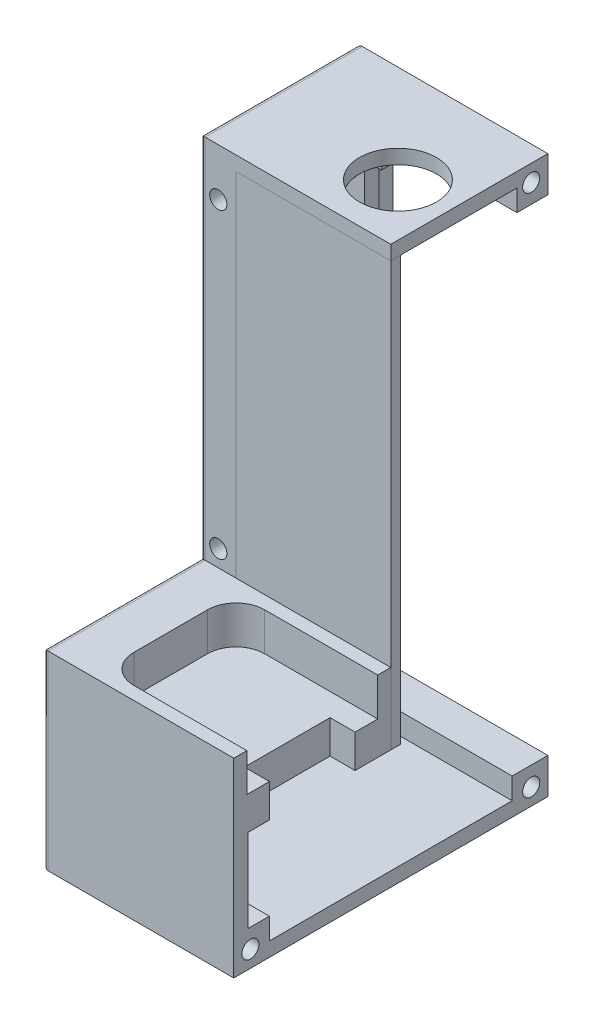
SolidWorks part; units mm, degrees
material "ABS"
ref_plane "Front" through (0, 0, 0) normal (0, 0, 1) x (1, 0, 0)
ref_plane "Top" through (0, 0, 0) normal (0, 1, 0) x (1, 0, 0)
ref_plane "Right" through (0, 0, 0) normal (1, 0, 0) x (0, 0, -1)
sketch "ｽｹｯﾁ1" plane through (0, 0, 0) normal (1, 0, 0) x (0, 0, -1)
  line L0 (23, 92) -> (0, 92)
  line L1 (33, 92) -> (23, 92)
  line L2 (33, 92) -> (33, -25)
  line L3 (33, -25) -> (23, -25)
  line L4 (23, 92) -> (23, -25)
  line L5 (0, 92) -> (0, -25)
  line L6 (0, -25) -> (23, -25)
  line L7 (0, -25) -> (-33, -25)
  line L8 (-33, -25) -> (-33, 0)
  line L9 (-33, 0) -> (0, 0)
  dimension "D1" = 117
  dimension "D2" = 10
  dimension "D3" = 33
  dimension "D4" = 23
  dimension "D5" = 25
extrude "ﾎﾞｽ - 押し出し1" add sketch "ｽｹｯﾁ1" along normal blind 60 contours L9 L8 L7 L5 | L5 L6 L4 L0 | L1 L4 L3 L2
sketch "ｽｹｯﾁ2" plane through (0, 0, -33) normal (0, 0, -1) x (-1, 0, 0)
  line L0 (-60, 92) -> (-60, -25) construction
  line L1 (-7.5, 22.5) -> (-52.5, 22.5)
  line L2 (-7.5, 22.5) -> (-7.5, 84.5)
  line L3 (-7.5, 84.5) -> (-52.5, 84.5)
  line L4 (-52.5, 22.5) -> (-52.5, 84.5)
  line L5 (-7.5, 22.5) -> (-52.5, 84.5) construction
  line L6 (-7.5, 84.5) -> (-52.5, 22.5) construction
  line L8 (0, 92) -> (0, -25) construction
  line L9 (-60, 92) -> (0, 92) construction
  point P0 (-30, 53.5)
  dimension "D1" = 62
  dimension "D2" = 7.5
  dimension "D3" = 7.5
  dimension "D4" = 7.5
extrude "ｶｯﾄ - 押し出し1" cut sketch "ｽｹｯﾁ2" against normal blind 10
sketch "ｽｹｯﾁ3" plane through (0, 92, 0) normal (0, 1, 0) x (1, 0, 0)
  line L1 (0, 33) -> (0, 0) construction
  line L2 (60, 0) -> (0, 0) construction
  circle A0 centre (29, 12.5) radius 8.1
  dimension "D1" = 16.2
  dimension "D2" = 29
  dimension "D3" = 12.5
extrude "ｶｯﾄ - 押し出し2" cut sketch "ｽｹｯﾁ3" against normal blind 10
sketch "ｽｹｯﾁ4" plane through (0, 0, -33) normal (0, 0, -1) x (-1, 0, 0)
  line L0 (-60, -25) -> (0, -25) construction
  line L1 (-7.5, 22.5) -> (-52.5, 22.5)
  line L2 (-7.5, 22.5) -> (-7.5, -17.5)
  line L3 (-7.5, -17.5) -> (-52.5, -17.5)
  line L4 (-52.5, 22.5) -> (-52.5, -17.5)
  line L7 (-60, 92) -> (-60, -25) construction
  dimension "D1" = 7.5
  dimension "D2" = 7.5
extrude "ｶｯﾄ - 押し出し3" cut sketch "ｽｹｯﾁ4" against normal offset from surface (58.5 mm away) 7.5 up to face at (30, -12.5, 33)
sketch "ｽｹｯﾁ5" plane through (0, 0, 0) normal (0, 1, 0) x (1, 0, 0)
  line L1 (41.75, -2.75) -> (16.25, -2.75)
  line L2 (47.75, -8.75) -> (47.75, -24.25)
  line L3 (41.75, -30.25) -> (16.25, -30.25)
  line L4 (10.25, -8.75) -> (10.25, -24.25)
  line L5 (47.75, -2.75) -> (10.25, -30.25) construction
  line L6 (47.75, -30.25) -> (10.25, -2.75) construction
  line L7 (0, -33) -> (0, 0) construction
  line L11 (60, -33) -> (0, -33)
  line L12 (60, -33) -> (60, 0)
  line L13 (60, 0) -> (0, 0)
  line L14 (0, -33) -> (0, 0)
  arc A0 (10.25, -8.75) -> (16.25, -2.75) centre (16.25, -8.75) cw
  arc A1 (47.75, -8.75) -> (41.75, -2.75) centre (41.75, -8.75) ccw
  arc A2 (47.75, -24.25) -> (41.75, -30.25) centre (41.75, -24.25) cw
  arc A3 (16.25, -30.25) -> (10.25, -24.25) centre (16.25, -24.25) cw
  point P0 (29, -16.5)
  dimension "D5" = 6
  dimension "D1" = 27.5
  dimension "D2" = 37.5
  dimension "D3" = 29
  dimension "D4" = 2.75
extrude "ﾎﾞｽ - 押し出し2" add sketch "ｽｹｯﾁ5" along normal blind 15
sketch "ｽｹｯﾁ6" plane through (0, 0, 0) normal (0, 1, 0) x (1, 0, 0)
  line L20 (34.75, -30.25) -> (34.75, -2.75)
  line L21 (42.75, -30.25) -> (42.75, -2.8339)
  line L22 (34.75, -25.5) -> (42.75, -25.5)
  line L24 (41.75, -2.75) -> (16.25, -2.75)
  line L25 (47.75, -24.25) -> (47.75, -8.75)
  line L26 (16.25, -30.25) -> (41.75, -30.25)
  line L27 (10.25, -8.75) -> (10.25, -24.25)
  line L28 (41.75, -2.75) -> (16.25, -2.75)
  line L29 (47.75, -24.25) -> (47.75, -8.75)
  line L30 (16.25, -30.25) -> (41.75, -30.25)
  line L31 (10.25, -8.75) -> (10.25, -24.25)
  line L32 (34.75, -7.5) -> (42.75, -7.5)
  arc A21 (16.25, -2.75) -> (10.25, -8.75) centre (16.25, -8.75) ccw
  arc A22 (47.75, -8.75) -> (41.75, -2.75) centre (41.75, -8.75) ccw
  arc A23 (41.75, -30.25) -> (47.75, -24.25) centre (41.75, -24.25) ccw
  arc A24 (10.25, -24.25) -> (16.25, -30.25) centre (16.25, -24.25) ccw
  arc A25 (16.25, -2.75) -> (10.25, -8.75) centre (16.25, -8.75) ccw
  arc A26 (47.75, -8.75) -> (41.75, -2.75) centre (41.75, -8.75) ccw
  arc A27 (41.75, -30.25) -> (47.75, -24.25) centre (41.75, -24.25) ccw
  arc A28 (10.25, -24.25) -> (16.25, -30.25) centre (16.25, -24.25) ccw
  arc M14 (10.3817, -25.5) -> (16.25, -30.25) centre (16.25, -24.25) ccw
  line M15 (16.25, -30.25) -> (41.75, -30.25)
  arc M16 (41.75, -30.25) -> (47.6183, -25.5) centre (41.75, -24.25) ccw
  line M17 (47.6183, -25.5) -> (10.3817, -25.5)
  dimension "D2" = 13
  dimension "D3" = 8
  dimension "D4" = 18
  dimension "D5" = 4.75
  dimension "D1" = 0
extrude "ﾎﾞｽ - 押し出し3" add sketch "ｽｹｯﾁ6" along normal blind 7 contours L31 A28 L20 L28 A25 M17 | L20 M15 M17 M14 | L21 L20 M16 M17 M15 | A27 L29 A26 L21 M17 | L21 M16 M17 | L21 A26 L28 L20 L32
sketch "ｽｹｯﾁ7" plane through (0, 0, 0) normal (0, 0, 1) x (1, 0, 0)
  line L0 (0, 92) -> (0, 15) construction
  line L1 (52.5, 89) -> (7.5, 89)
  line L2 (52.5, 89) -> (52.5, 22.5)
  line L3 (52.5, 22.5) -> (7.5, 22.5)
  line L4 (7.5, 89) -> (7.5, 22.5)
  line L5 (52.5, 89) -> (7.5, 22.5) construction
  line L6 (52.5, 22.5) -> (7.5, 89) construction
  line L7 (60, 92) -> (0, 92) construction
  line L9 (52.5, 22.5) -> (7.5, 22.5) construction
  line L11 (52.5, 22.5) -> (52.5, 15) construction
  point P0 (30, 55.75)
  dimension "D1" = 7.5
  dimension "D2" = 3
extrude "ｶｯﾄ - 押し出し4" cut sketch "ｽｹｯﾁ7" against normal offset from surface (20 mm away) 3 up to face at (30, 53.5, -23)
sketch "ｽｹｯﾁ8" plane through (0, 89, 0) normal (0, -1, 0) x (-1, 0, 0)
  line L1 (-7.5, 0) -> (-52.5, 0)
  line L2 (-7.5, 0) -> (-7.5, 2)
  line L3 (-7.5, 2) -> (-52.5, 2)
  line L4 (-52.5, 0) -> (-52.5, 2)
  line L6 (-52.5, 20) -> (-52.5, 0) construction
  dimension "D1" = 2
extrude "ﾎﾞｽ - 押し出し4" add sketch "ｽｹｯﾁ8" along normal up to vertex (89 mm away) separate body
sketch "ｽｹｯﾁ9" plane through (0, 0, 0) normal (-1, 0, 0) x (0, 0, 1)
  line L0 (-33, 92) -> (0, 92) construction
  line L1 (-33, 92) -> (-33, -25) construction
  line L2 (-33, -25) -> (33, -25) construction
  line L3 (33, -25) -> (33, 15) construction
  circle A0 centre (-29.5, 88.5) radius 1.8
  circle A1 centre (-29.5, -21.5) radius 1.8
  circle A2 centre (29.5, -21.5) radius 1.8
  dimension "D3" = 3.6
  dimension "D5" = 3.5
  dimension "D1" = 3.5
  dimension "D2" = 3.5
  dimension "D4" = 3.5
extrude "ｶｯﾄ - 押し出し5" cut sketch "ｽｹｯﾁ9" against normal through all
sketch "ｽｹｯﾁ10" plane through (0, 0, 0) normal (0, 0, 1) x (1, 0, 0)
  line L0 (60, 92) -> (0, 92) construction
  line L1 (7.5, 15) -> (0, 15) construction
  line L2 (0, 92) -> (0, 15) construction
  line L3 (60, 92) -> (60, 15) construction
  circle A0 centre (3.75, 82) radius 1.8
  circle A1 centre (56.25, 82) radius 1.8
  circle A2 centre (56.25, 18.5) radius 1.8
  circle A3 centre (3.75, 18.5) radius 1.8
  dimension "D3" = 3.6
  dimension "D1" = 3.5
  dimension "D2" = 10
  dimension "D4" = 3.75
  dimension "D5" = 3.75
extrude "ｶｯﾄ - 押し出し6" cut sketch "ｽｹｯﾁ10" against normal through all both and the other way through all
sketch "ｽｹｯﾁ12" plane through (0, 0, -23) normal (0, 0, -1) x (-1, 0, 0)
  line L0 (-52.5, 84.5) -> (-52.5, 22.5) construction
  line L2 (-7.5, 84.5) -> (-52.5, 84.5) construction
  circle A0 centre (-49, 81.5) radius 1.8
  circle A1 centre (-11, 81.5) radius 1.8
  circle A2 centre (-11, 39.5) radius 1.8
  circle A3 centre (-49, 39.5) radius 1.8
  dimension "D3" = 3.6
  dimension "D1" = 42
  dimension "D2" = 38
  dimension "D4" = 3.5
  dimension "D5" = 3
extrude "ｶｯﾄ - 押し出し7" cut sketch "ｽｹｯﾁ12" against normal up to next (3 mm away)
sketch "ｽｹｯﾁ15" plane through (60, 0, 0) normal (1, 0, 0) x (0, 0, -1)
  line L6 (0, 15) -> (-33, 15)
  line L13 (-33, 15) -> (-33, -25)
  line L14 (-33, -25) -> (33, -25)
  line L15 (33, -25) -> (33, 92)
  line L19 (-33, 15) -> (-33, -25)
  line L20 (-33, -25) -> (33, -25)
  line L21 (33, -25) -> (33, 92)
  line L26 (33, 92) -> (0, 92)
  line L28 (33, 92) -> (0, 92)
  line L30 (0, 15) -> (-33, 15)
  line L32 (0, 92) -> (0, 15)
  line L34 (0, 92) -> (0, 15)
  dimension "D1" = 0
extrude "ｶｯﾄ - 押し出し9" cut sketch "ｽｹｯﾁ15" against normal blind 20
sketch "ｽｹｯﾁ17" plane through (0, -17.5, 0) normal (0, 1, 0) x (1, 0, 0)
  line L0 (40, -25.5) -> (40, 33) construction
  line L1 (7.5, -25.5) -> (40, -25.5)
  line L2 (7.5, -25.5) -> (7.5, 25.5)
  line L3 (7.5, 25.5) -> (40, 25.5)
  line L4 (40, -25.5) -> (40, 25.5)
  line L5 (40, 33) -> (7.5, 33) construction
  dimension "D1" = 7.5
extrude "ｶｯﾄ - 押し出し11" cut sketch "ｽｹｯﾁ17" against normal offset from surface (4.5 mm away) 3 up to face at (20, -25, 0)
sketch "ｽｹｯﾁ18" plane through (0, 0, 25.5) normal (0, 0, -1) x (-1, 0, 0)
  line L0 (-40, 7) -> (-40, -22) construction
  line L1 (-7.5, 0) -> (-40, 0)
  line L2 (-7.5, 0) -> (-7.5, -17.5)
  line L3 (-7.5, -17.5) -> (-40, -17.5)
  line L4 (-40, 0) -> (-40, -17.5)
  line L6 (-40, -25) -> (0, -25) construction
  dimension "D1" = 7.5
extrude "ｶｯﾄ - 押し出し12" cut sketch "ｽｹｯﾁ18" against normal offset from surface (4.5 mm away) 3 up to face at (20, -5, 33)
sketch "ｽｹｯﾁ19" plane through (0, 0, -23) normal (0, 0, -1) x (-1, 0, 0)
  line L1 (-40, 84.5) -> (-14.5, 84.5)
  line L2 (-40, 84.5) -> (-40, 22.5)
  line L3 (-40, 22.5) -> (-14.5, 22.5)
  line L4 (-14.5, 84.5) -> (-14.5, 22.5)
  line L6 (-7.5, 22.5) -> (-7.5, 84.5) construction
  dimension "D1" = 7
extrude "ｶｯﾄ - 押し出し13" cut sketch "ｽｹｯﾁ19" against normal up to next (3 mm away)
sketch "ｽｹｯﾁ20" plane through (40, 0, 0) normal (1, 0, 0) x (0, 0, -1)
  line L0 (20, 84.5) -> (33, 84.5) construction
  line L1 (20, 89) -> (26.5, 89)
  line L2 (20, 89) -> (20, 84.5)
  line L3 (20, 84.5) -> (26.5, 84.5)
  line L4 (26.5, 89) -> (26.5, 84.5)
extrude "ｶｯﾄ - 押し出し14" cut sketch "ｽｹｯﾁ20" against normal offset from surface (22 mm away) 3.5 up to face at (14.5, 53.5, -21.5)
fillet "ﾌｨﾚｯﾄ1" radius 1 6 edges at (0, -25, 0) (0, -5, 33) (0, 15, 16.5) (0, 53.5, 0) (0, 92, -16.5) (0, 33.5, -33)
